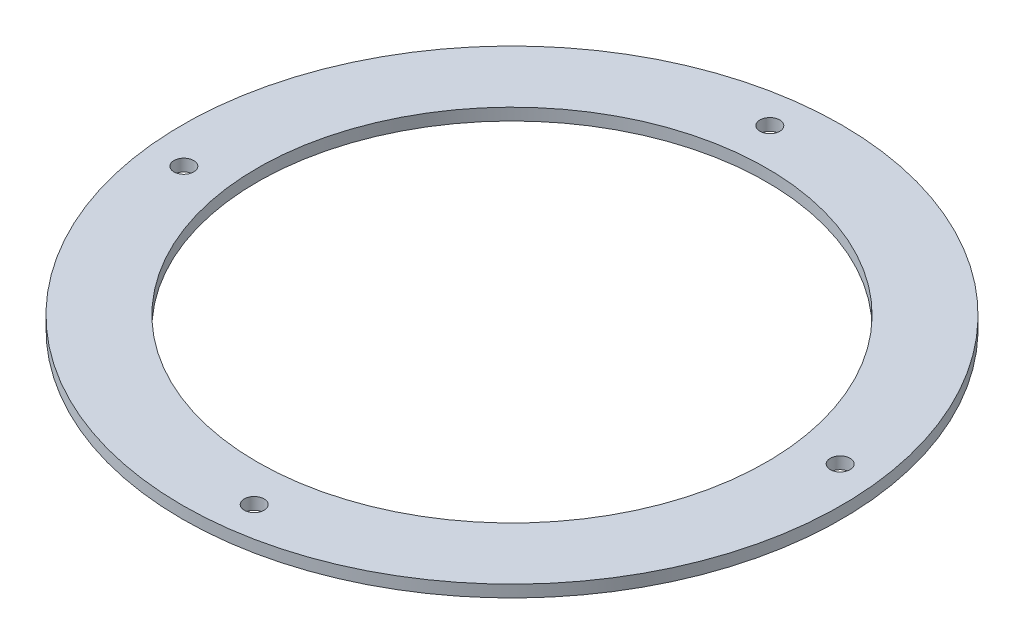
SolidWorks part; units mm, degrees
ref_plane "前视基准面" through (0, 0, 0) normal (0, 0, 1) x (1, 0, 0)
ref_plane "上视基准面" through (0, 0, 0) normal (0, 1, 0) x (1, 0, 0)
ref_plane "右视基准面" through (0, 0, 0) normal (1, 0, 0) x (0, 0, -1)
sketch "草图1" plane through (0, 0, 0) normal (0, 1, 0) x (1, 0, 0)
  circle A0 centre (0, 0) radius 55
extrude "凸台-拉伸1" add sketch "草图1" along normal blind 2
sketch "草图2" plane through (0, 2, 0) normal (0, 1, 0) x (1, 0, 0)
  line L1 (48.899, 5.8696) -> (-5.8696, 48.899)
  line L2 (-5.8696, 48.899) -> (-48.899, -5.8696)
  line L3 (-48.899, -5.8696) -> (5.8696, -48.899)
  line L4 (5.8696, -48.899) -> (48.899, 5.8696)
  circle A0 centre (0, 0) radius 49.25 construction
  circle A1 centre (-48.899, -5.8696) radius 1.65
  circle A2 centre (-5.8696, 48.899) radius 1.65
  circle A3 centre (48.899, 5.8696) radius 1.65
  circle A4 centre (5.8696, -48.899) radius 1.65
extrude "切除-拉伸1" cut sketch "草图2" against normal blind 14 contours A1 | A2 | A3 | A4
sketch "草图3" plane through (0, 2, 0) normal (0, 1, 0) x (1, 0, 0)
  circle A0 centre (0, 0) radius 42.5
extrude "切除-拉伸2" cut sketch "草图3" against normal blind 14
